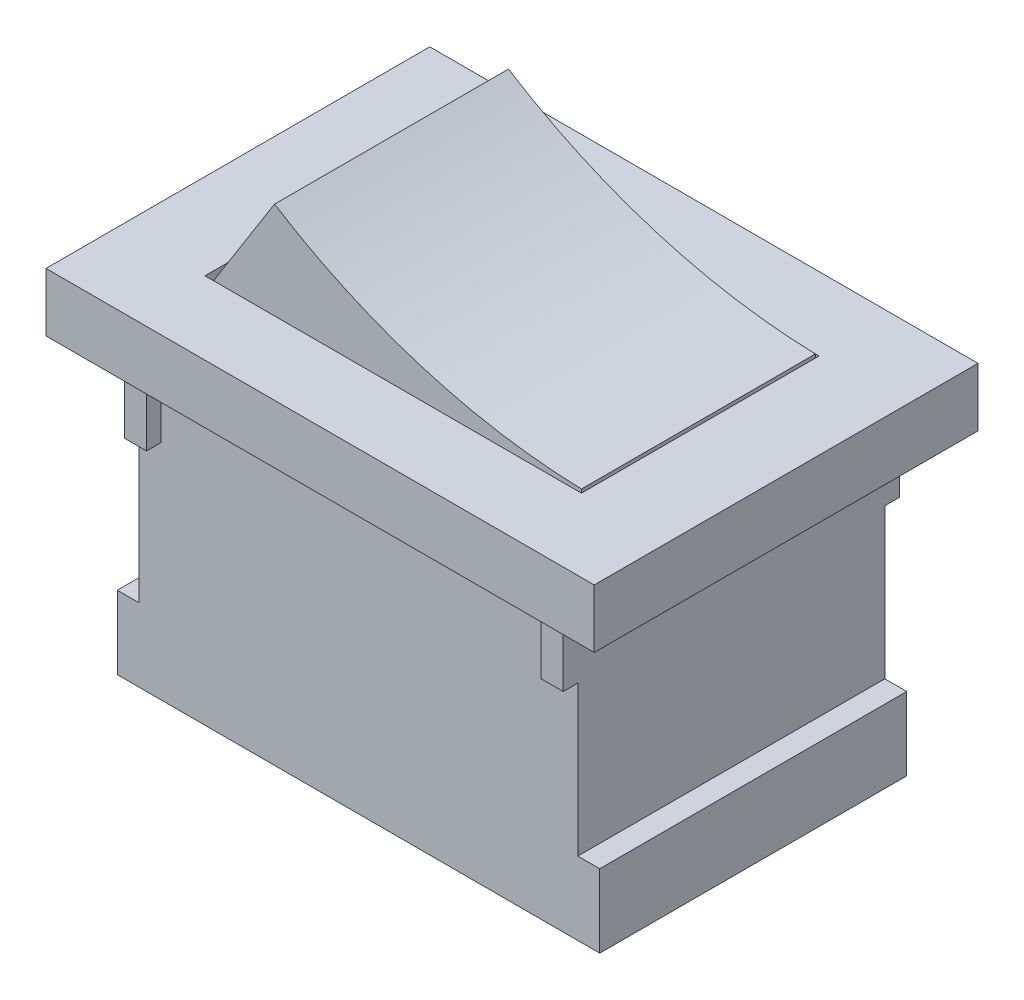
SolidWorks part; units mm, degrees
ref_plane "Front Plane" through (0, 0, 0) normal (0, 0, 1) x (1, 0, 0)
ref_plane "Top Plane" through (0, 0, 0) normal (0, 1, 0) x (1, 0, 0)
ref_plane "Right Plane" through (0, 0, 0) normal (1, 0, 0) x (0, 0, -1)
sketch "Sketch1" plane through (0, 0, 0) normal (0, 1, 0) x (1, 0, 0)
  line L1 (-7.5, -5.25) -> (7.5, -5.25)
  line L2 (-7.5, -5.25) -> (-7.5, 5.25)
  line L3 (-7.5, 5.25) -> (7.5, 5.25)
  line L4 (7.5, -5.25) -> (7.5, 5.25)
  line L5 (-7.5, -5.25) -> (7.5, 5.25) construction
  line L6 (-7.5, 5.25) -> (7.5, -5.25) construction
  point P0 (0, 0)
  dimension "D1" = 15
  dimension "D2" = 10.5
extrude "Boss-Extrude1" add sketch "Sketch1" along normal blind 1.6
sketch "Sketch2" plane through (0, 1.6, 0) normal (0, 1, 0) x (1, 0, 0)
  line L1 (-5.15, 3.25) -> (5.15, 3.25)
  line L2 (-5.15, 3.25) -> (-5.15, -3.25)
  line L3 (-5.15, -3.25) -> (5.15, -3.25)
  line L4 (5.15, 3.25) -> (5.15, -3.25)
  line L5 (-5.15, 3.25) -> (5.15, -3.25) construction
  line L6 (-5.15, -3.25) -> (5.15, 3.25) construction
  point P0 (0, 0)
  dimension "D1" = 10.3
  dimension "D2" = 6.5
extrude "Cut-Extrude1" cut sketch "Sketch2" against normal blind 1.5
sketch "Sketch3" plane through (0, 0.1, 0) normal (0, 1, 0) x (1, 0, 0)
  line L1 (-5.1, -3.2) -> (5.1, -3.2)
  line L2 (-5.1, -3.2) -> (-5.1, 3.2)
  line L3 (-5.1, 3.2) -> (5.1, 3.2)
  line L4 (5.1, -3.2) -> (5.1, 3.2)
  line L5 (-5.1, -3.2) -> (5.1, 3.2) construction
  line L6 (-5.1, 3.2) -> (5.1, -3.2) construction
  point P0 (0, 0)
  dimension "D1" = 10.2
  dimension "D2" = 6.4
extrude "Boss-Extrude2" add sketch "Sketch3" along normal blind 4.1
sketch "Sketch4" plane through (0, 0, 3.2) normal (0, 0, 1) x (1, 0, 0)
  line L0 (-5.1, 1.3383) -> (-3.2966, 4.2)
  line L1 (-5.1, 4.2) -> (5.1, 4.2) construction
  line L2 (5.1, 4.2) -> (5.1, 0.1) construction
  line L7 (-5.1, 0.1) -> (5.1, 0.1)
  line L8 (5.1, 0.1) -> (5.1, 4.2)
  line L9 (5.1, 4.2) -> (-5.1, 4.2)
  line L10 (-5.1, 4.2) -> (-5.1, 0.1)
  line L11 (-5.1, 0.1) -> (5.1, 0.1)
  line L12 (5.1, 0.1) -> (5.1, 4.2)
  line L13 (5.1, 4.2) -> (-5.1, 4.2)
  line L14 (-5.1, 4.2) -> (-5.1, 0.1)
  arc A0 (-3.2966, 4.2) -> (5.1, 1.648) centre (5.5618, 18.2566) ccw
  line M8 (5.1, 4.2) -> (-5.1, 4.2)
  line M9 (-5.1, 4.2) -> (-5.1, 0.1)
  dimension "D1" = 0
extrude "Cut-Extrude4" cut sketch "Sketch4" against normal blind 6.4 contours L0 M9 M8 | A0 L12 M8
sketch "Sketch8" plane through (0, 0, 0) normal (0, -1, 0) x (-1, 0, 0)
  line L1 (-6.6, 4.2) -> (6.6, 4.2)
  line L2 (-6.6, 4.2) -> (-6.6, -4.2)
  line L3 (-6.6, -4.2) -> (6.6, -4.2)
  line L4 (6.6, 4.2) -> (6.6, -4.2)
  line L5 (-6.6, 4.2) -> (6.6, -4.2) construction
  line L6 (-6.6, -4.2) -> (6.6, 4.2) construction
  point P0 (0, 0)
  dimension "D1" = 8.4
  dimension "D2" = 13.2
extrude "Boss-Extrude5" add sketch "Sketch8" along normal blind 8.1 separate body
sketch "Sketch9" plane through (0, 0, 4.2) normal (0, 0, 1) x (1, 0, 0)
  line L0 (-6.6, 0) -> (-6, 0)
  line L1 (6.6, 0) -> (-6.6, 0) construction
  line L2 (-6, 0) -> (-6, -6.1)
  line L3 (-6, -6.1) -> (-6.6, -6.1)
  line L4 (-6.6, -8.1) -> (-6.6, 0) construction
  line L5 (-6.6, -6.1) -> (-6.6, 0)
  line L6 (-7.5, 1.6) -> (-7.5, 0) construction
  line L7 (6.6, -8.1) -> (-6.6, -8.1) construction
  line L8 (0, 0) -> (0, -8.1) construction
  line L9 (-7.5, 0) -> (7.5, 0) construction
  line L10 (6, -6.1) -> (6.6, -6.1)
  line L11 (6, 0) -> (6, -6.1)
  line L12 (6.6, 0) -> (6, 0)
  line L13 (6.6, -6.1) -> (6.6, 0)
  point P11 (-6.3, -6.1)
  dimension "D1" = 1.5
  dimension "D2" = 2
extrude "Cut-Extrude30" cut sketch "Sketch9" against normal blind 8.4
sketch "Sketch10" plane through (0, 0, -4.2) normal (0, 0, -1) x (-1, 0, 0)
  line L0 (-6, 0) -> (-5.4, 0)
  line L1 (6, 0) -> (-6, 0) construction
  line L2 (-5.4, 0) -> (-5.4, -2)
  line L3 (-5.4, -2) -> (-6, -2)
  line L4 (-6, 0) -> (-6, -6.1) construction
  line L5 (-6, -2) -> (-6, 0)
  line L6 (0, -0.3195) -> (0, 0)
  line L7 (5.4, -2) -> (6, -2)
  line L8 (5.4, 0) -> (5.4, -2)
  line L9 (6, 0) -> (5.4, 0)
  line L10 (6, -2) -> (6, 0)
  line L19 (6, 0) -> (-6, 0)
  line L20 (6, -6.1) -> (6, 0)
  line L21 (6.6, -6.1) -> (6, -6.1)
  line L22 (6.6, -8.1) -> (6.6, -6.1)
  line L23 (-6.6, -8.1) -> (6.6, -8.1)
  line L24 (-6.6, -6.1) -> (-6.6, -8.1)
  line L25 (-6, -6.1) -> (-6.6, -6.1)
  line L26 (-6, 0) -> (-6, -6.1)
  line L27 (6, 0) -> (-6, 0)
  line L28 (6, -6.1) -> (6, 0)
  line L29 (6.6, -6.1) -> (6, -6.1)
  line L30 (6.6, -8.1) -> (6.6, -6.1)
  line L31 (-6.6, -8.1) -> (6.6, -8.1)
  line L32 (-6.6, -6.1) -> (-6.6, -8.1)
  line L33 (-6, -6.1) -> (-6.6, -6.1)
  line L34 (-6, 0) -> (-6, -6.1)
  line M8 (6, 0) -> (-6, 0)
  line M9 (-6, 0) -> (-6, -6.1)
  dimension "D1" = 2
  dimension "D2" = 0.6
  dimension "D3" = 0
extrude "Boss-Extrude7" add sketch "Sketch10" along normal blind 0.4 contours L3 L2 M8 M9 | L9 L8 L7 L10
pattern_linear "LPattern3" count 2 spacing 8.8 along (0, 0, 1) of "Boss-Extrude7"
sketch "Sketch12" plane through (-6, 0, 0) normal (-1, 0, 0) x (0, 0, 1)
  line L1 (-0.8599, -0.0228) -> (0.8599, -0.0228)
  line L2 (-0.8599, -0.0228) -> (-0.8599, -6.0681)
  line L3 (-0.8599, -6.0681) -> (0.8599, -6.0681)
  line L4 (0.8599, -0.0228) -> (0.8599, -6.0681)
  line L5 (-0.8599, -0.0228) -> (0.8599, -6.0681) construction
  line L6 (-0.8599, -6.0681) -> (0.8599, -0.0228) construction
  point P0 (0, -3.0454)
extrude "Boss-Extrude8" add sketch "Sketch12" along normal blind 1.1
sketch "Sketch14" plane through (0, 0, -0.8599) normal (0, 0, -1) x (-1, 0, 0)
  line L0 (6, -0.0228) -> (6.59, -3.0675)
  line L1 (6.59, -3.0675) -> (6, -6.0681)
  line L2 (6.4225, -0.0228) -> (7.0127, -3.0681)
  line L3 (7.0127, -3.0681) -> (6.4228, -6.0681)
  line L4 (6.4072, 0.0561) -> (7.0127, -3.0681) construction
  line L5 (7.0127, -3.0681) -> (6.407, -6.1481) construction
  line L6 (7.1, -6.0681) -> (6, -6.0681) construction
  line L7 (6, -6.1) -> (6, -2) construction
  line L9 (7.1, -0.0228) -> (6, -0.0228) construction
  line L14 (6, -0.0228) -> (6, -6.0681)
  line L15 (7.1, -0.0228) -> (6, -0.0228)
  line L16 (7.1, -6.0681) -> (7.1, -0.0228)
  line L17 (6, -6.0681) -> (7.1, -6.0681)
  line L18 (6, -0.0228) -> (6, -6.0681)
  line L19 (7.1, -0.0228) -> (6, -0.0228)
  line L20 (7.1, -6.0681) -> (7.1, -0.0228)
  line L21 (6, -6.0681) -> (7.1, -6.0681)
  dimension "D1" = 0.59
  dimension "D2" = 3
  dimension "D3" = 1.0127
  dimension "D4" = 0
extrude "Cut-Extrude42" cut sketch "Sketch14" against normal blind 1.1 contours L2 L3 L1 L4 L5
